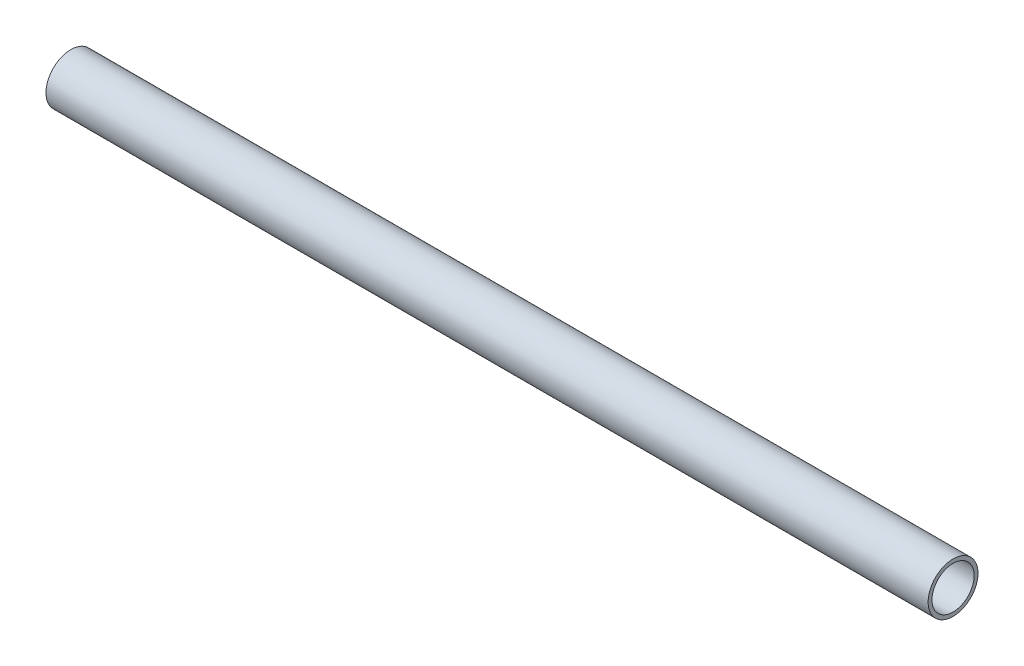
SolidWorks part; units mm, degrees
material "普通碳钢"
ref_plane "前视基准面" through (0, 0, 0) normal (0, 0, 1) x (1, 0, 0)
ref_plane "上视基准面" through (0, 0, 0) normal (0, 1, 0) x (1, 0, 0)
ref_plane "右视基准面" through (0, 0, 0) normal (1, 0, 0) x (0, 0, -1)
sketch "草图1" plane through (0, 0, 0) normal (1, 0, 0) x (0, 0, -1)
  circle A0 centre (0, 0) radius 13
  circle A1 centre (0, 0) radius 11
  dimension "D1" = 22
  dimension "D2" = 26
extrude "凸台-拉伸1" add sketch "草图1" along normal blind 460
sketch "草图2" plane through (0, 0, 0) normal (0, 0, 1) x (1, 0, 0)
  line L0 (0, 0) -> (64.4782, 0) construction
  line L1 (0, 13) -> (0, -13) construction
  line L2 (460, -13) -> (460, 13) construction
  circle A0 centre (21, 0) radius 2
  circle A1 centre (445, 0) radius 2.5
  dimension "D1" = 4
  dimension "D3" = 15
  dimension "D2" = 21
extrude "切除-拉伸1" cut sketch "草图2" against normal through all
